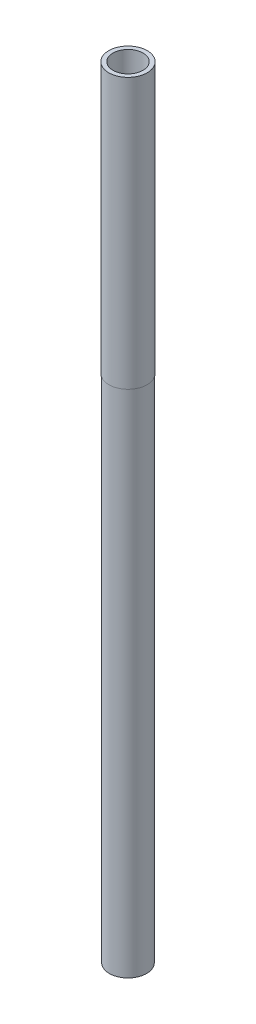
SolidWorks part; units mm, degrees
ref_plane "Front Plane" through (0, 0, 0) normal (0, 0, 1) x (1, 0, 0)
ref_plane "Top Plane" through (0, 0, 0) normal (0, 1, 0) x (1, 0, 0)
ref_plane "Right Plane" through (0, 0, 0) normal (1, 0, 0) x (0, 0, -1)
sketch "Sketch1" plane through (0, 0, 0) normal (0, 1, 0) x (1, 0, 0)
  circle A0 centre (0, 0) radius 0.25
  circle A1 centre (0, 0) radius 0.31
extrude "Boss-Extrude1" add sketch "Sketch1" along normal blind 13
sketch "Sketch2" plane through (0, 13, 0) normal (0, 1, 0) x (1, 0, 0)
  circle A1 centre (0, 0) radius 0.31 construction
  circle A2 centre (0, 0) radius 0.31
  circle A3 centre (0, 0) radius 0.32
  dimension "D1" = 0.01
extrude "Boss-Extrude2" add sketch "Sketch2" against normal blind 4.5
